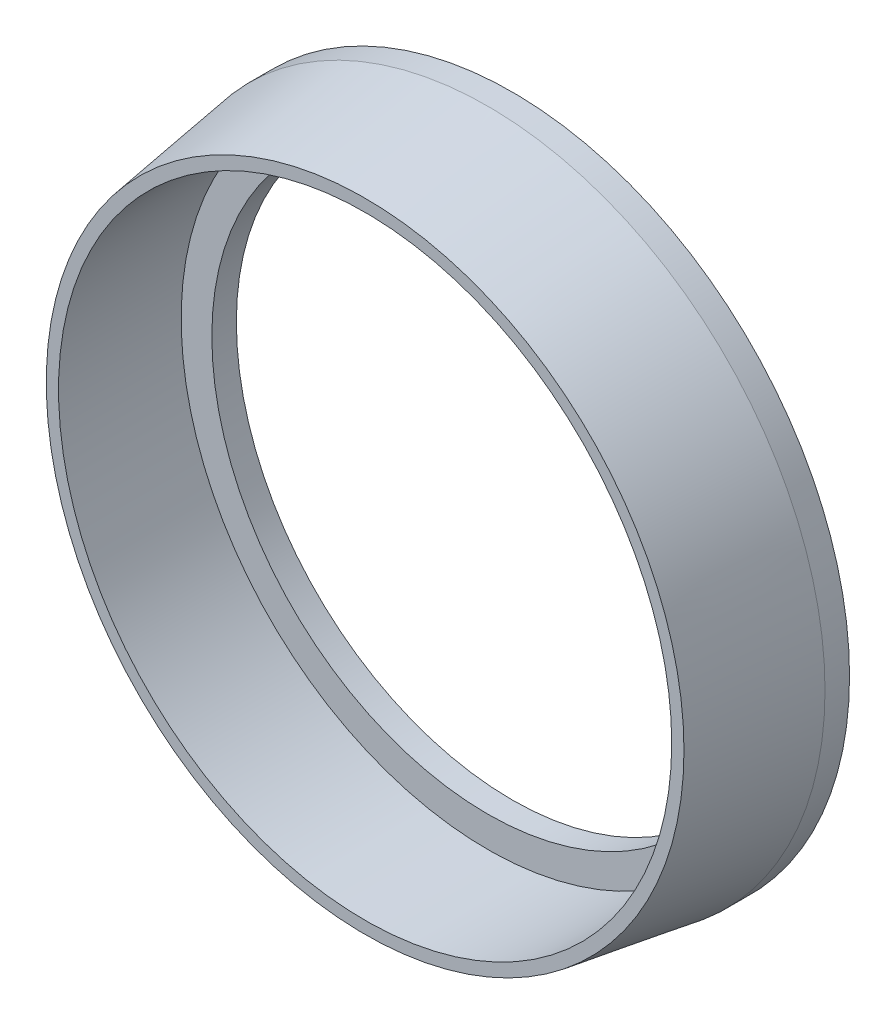
SolidWorks part; units mm, degrees
ref_plane "前基準面" through (0, 0, 0) normal (0, 0, 1) x (1, 0, 0)
ref_plane "上基準面" through (0, 0, 0) normal (0, 1, 0) x (1, 0, 0)
ref_plane "右基準面" through (0, 0, 0) normal (1, 0, 0) x (0, 0, -1)
sketch "草圖1" plane through (0, 0, 0) normal (0, 0, 1) x (1, 0, 0)
  circle A0 centre (0, 0) radius 27.5
  circle A1 centre (0, 0) radius 22.5
  dimension "D1" = 55
  dimension "D2" = 45
ref_plane "平面1" through (0, 0, 10) normal (0, 0, 1) x (1, 0, 0)
sketch "草圖2" plane through (0, 0, 10) normal (0, 0, 1) x (1, 0, 0)
  line L1 (0, 25) -> (0, -25) construction
  circle A0 centre (0, 0) radius 25
  dimension "D1" = 50
sketch "草圖5" plane through (0, 0, 0) normal (1, 0, 0) x (0, 0, -1)
  line L0 (0, 27.5) -> (0, -27.5) construction
  line L3 (0, 27.5) -> (0, -27.5) construction
  line L5 (-10, 25) -> (-10, -25) construction
  line L6 (-10, 0) -> (0, 0)
  line L8 (-10, 25) -> (-10, 26)
  line L9 (-10, 25) -> (0, 25)
  line L10 (0, 25) -> (0, 27.5)
  line L11 (-10, 26) -> (0, 27.5)
revolve "旋轉2" add sketch "草圖5" angle 360 about L6
extrude "填料-伸長1" add sketch "草圖1" against normal blind 2
